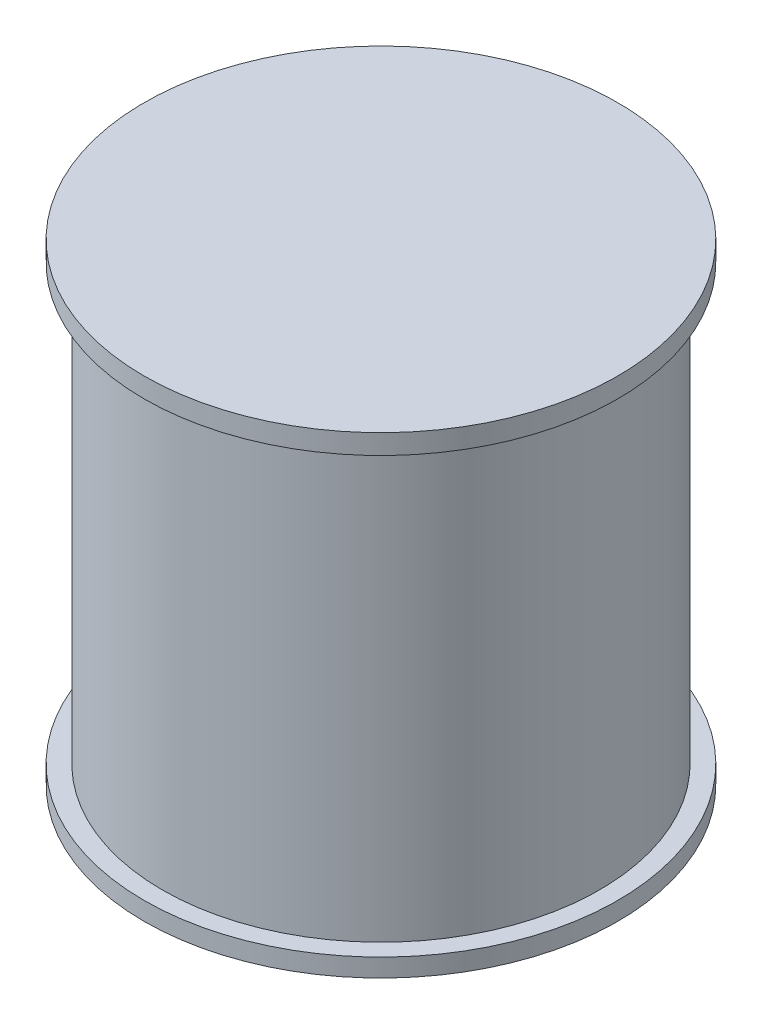
SolidWorks part; units mm, degrees
ref_plane "Alzado" through (0, 0, 0) normal (0, 0, 1) x (1, 0, 0)
ref_plane "Planta" through (0, 0, 0) normal (0, 1, 0) x (1, 0, 0)
ref_plane "Vista lateral" through (0, 0, 0) normal (1, 0, 0) x (0, 0, -1)
sketch "Croquis1" plane through (0, 0, 0) normal (0, 0, 1) x (1, 0, 0)
  line L0 (0, 38.8006) -> (0, -62.5731)
  line L1 (0, -62.5731) -> (50.8215, -62.5731)
  line L2 (50.8215, -62.5731) -> (50.8215, -58.6741)
  line L3 (50.8215, -58.6741) -> (46.9225, -58.6741)
  line L4 (46.9225, -58.6741) -> (46.9225, 34.5472)
  line L5 (46.9225, 34.5472) -> (50.8215, 34.5472)
  line L6 (50.8215, 34.5472) -> (50.8215, 38.8006)
  line L7 (50.8215, 38.8006) -> (0, 38.8006)
  dimension "D7" = 4.2534
  dimension "D1" = 101.3738
  dimension "D2" = 50.8215
  dimension "D3" = 3.899
  dimension "D4" = 3.899
  dimension "D5" = 93.2213
  dimension "D6" = 3.899
  dimension "D8" = 50.8215
revolve "Revolución1" add sketch "Croquis1" angle 360 about L0
ref_plane "Plano1" through (0, 0, 0) normal (0, 0, 1) x (1, 0, 0)
sketch "Croquis3" plane through (0, 0, 0) normal (0, 0, 1) x (1, 0, 0)
  line L0 (50.8215, -58.6741) -> (-50.8215, -58.6741) construction
  line L1 (-46.8969, 34.5263) -> (-44.3969, 34.5263)
  line L2 (-46.8969, 34.5263) -> (-46.8969, -58.6741)
  line L3 (-46.8969, -58.6741) -> (-44.3969, -58.6741)
  line L4 (-44.3969, 34.5263) -> (-44.3969, -58.6741)
  line L5 (-46.9225, 34.5472) -> (46.9225, 34.5472) construction
  line L6 (-41.3745, 34.5472) -> (-38.8745, 34.5472)
  line L7 (-41.3745, 34.5472) -> (-41.3745, -58.6741)
  line L8 (-41.3745, -58.6741) -> (-38.8745, -58.6741)
  line L9 (-38.8745, 34.5472) -> (-38.8745, -58.6741)
  dimension "D1" = 2.5
  dimension "D2" = 2.5
extrude "Saliente-Extruir1" add sketch "Croquis3" against normal blind 25 draft 1
